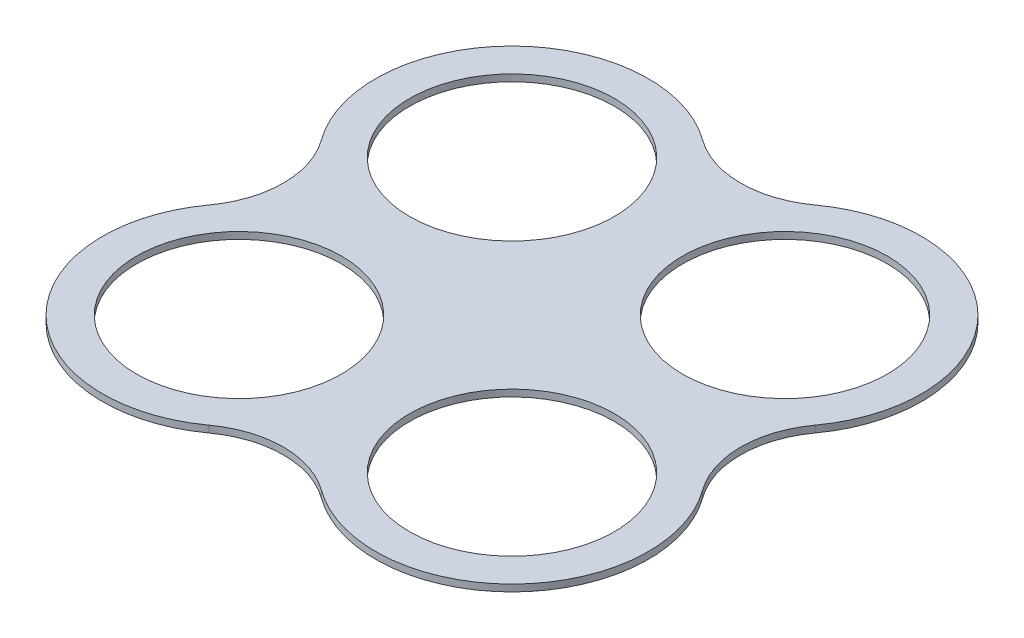
SolidWorks part; units mm, degrees
material "Beech"
ref_plane "Front Plane" through (0, 0, 0) normal (0, 0, 1) x (1, 0, 0)
ref_plane "Top Plane" through (0, 0, 0) normal (0, 1, 0) x (1, 0, 0)
ref_plane "Right Plane" through (0, 0, 0) normal (1, 0, 0) x (0, 0, -1)
sketch "Sketch1" plane through (0, 0, 0) normal (0, 1, 0) x (1, 0, 0)
  line L0 (-102.7036, -74.7059) -> (-102.7036, -179.2941) construction
  line L1 (356.7036, -74.7059) -> (356.7036, -179.2941) construction
  line L2 (179.2941, -356.7036) -> (74.7059, -356.7036) construction
  line L3 (179.2941, 102.7036) -> (74.7059, 102.7036) construction
  line L4 (127, 85.6961) -> (127, -339.6961) construction
  line L5 (339.6961, -127) -> (-85.6961, -127) construction
  arc A0 (74.7059, 102.7036) -> (-102.7036, -74.7059) centre (0, 0) ccw
  arc A1 (356.7036, -74.7059) -> (179.2941, 102.7036) centre (254, 0) ccw
  arc A2 (74.7059, 102.7036) -> (179.2941, 102.7036) centre (127, 174.5961) ccw
  arc A3 (-102.7036, -179.2941) -> (74.7059, -356.7036) centre (0, -254) ccw
  arc A4 (179.2941, -356.7036) -> (356.7036, -179.2941) centre (254, -254) ccw
  arc A5 (179.2941, -356.7036) -> (74.7059, -356.7036) centre (127, -428.5961) ccw
  arc A6 (-102.7036, -179.2941) -> (-102.7036, -74.7059) centre (-174.5961, -127) ccw
  arc A7 (356.7036, -74.7059) -> (356.7036, -179.2941) centre (428.5961, -127) ccw
  circle A8 centre (0, 0) radius 95.25
  circle A9 centre (254, 0) radius 95.25
  circle A10 centre (254, -254) radius 95.25
  circle A11 centre (0, -254) radius 95.25
  point P4 (127, -127)
  dimension "D1" = 254
  dimension "D2" = 177.8
  dimension "D5" = 190.5
extrude "Boss-Extrude1" add sketch "Sketch1" along normal blind 6.35
sketch "Sketch2" plane through (0, 6.35, 0) normal (0, 1, 0) x (1, 0, 0)
  line L0 (127, 85.6961) -> (127, -339.6961) construction
  arc A0 (74.7059, 102.7036) -> (179.2941, 102.7036) centre (127, 174.5961) ccw construction
  arc A1 (179.2941, -356.7036) -> (74.7059, -356.7036) centre (127, -428.5961) ccw construction
